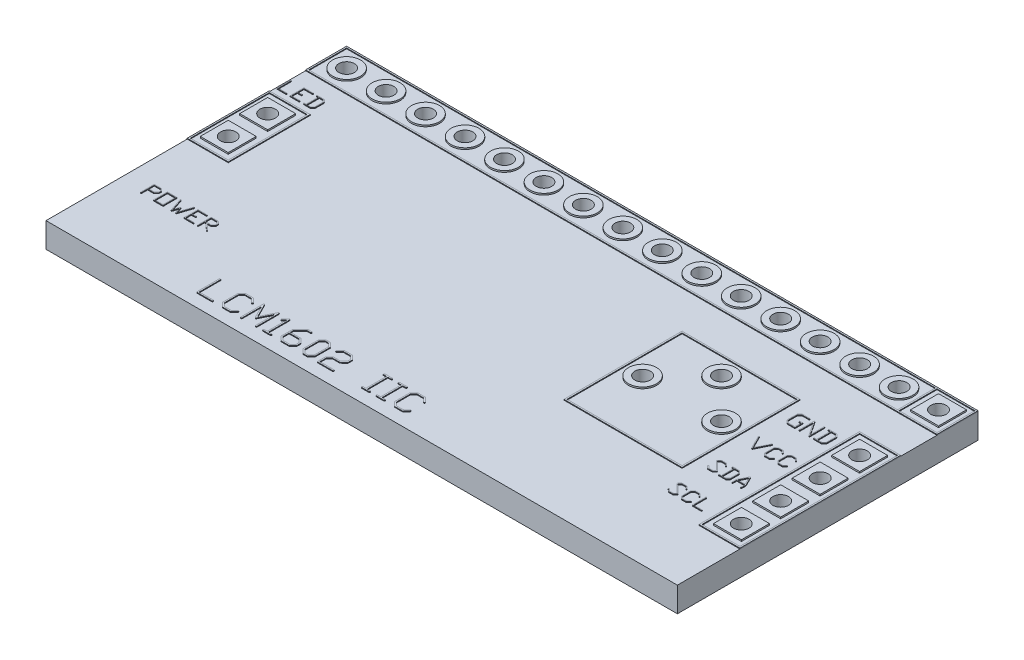
SolidWorks part; units mm, degrees
material "E-Glass Fiber"
ref_plane "Front Plane" through (0, 0, 0) normal (0, 0, 1) x (1, 0, 0)
ref_plane "Top Plane" through (0, 0, 0) normal (0, 1, 0) x (1, 0, 0)
ref_plane "Right Plane" through (0, 0, 0) normal (1, 0, 0) x (0, 0, -1)
sketch "Sketch2" plane through (0, 0, 0) normal (0, 1, 0) x (1, 0, 0)
  line L0 (-1.27, 1.27) -> (1.27, -1.27) construction
  line L1 (-1.27, 1.27) -> (1.27, 1.27)
  line L2 (-1.27, 1.27) -> (-1.27, -1.27)
  line L3 (-1.27, -1.27) -> (1.27, -1.27)
  line L4 (1.27, 1.27) -> (1.27, -1.27)
  line L5 (1.27, 1.27) -> (3.81, 1.27)
  line L6 (1.27, 1.27) -> (1.27, -1.27)
  line L7 (3.81, 1.27) -> (3.81, -1.27)
  line L8 (1.27, -1.27) -> (3.81, -1.27)
  line L9 (3.81, 1.27) -> (6.35, 1.27)
  line L10 (3.81, 1.27) -> (3.81, -1.27)
  line L11 (6.35, 1.27) -> (6.35, -1.27)
  line L12 (3.81, -1.27) -> (6.35, -1.27)
  line L13 (6.35, 1.27) -> (8.89, 1.27)
  line L14 (6.35, 1.27) -> (6.35, -1.27)
  line L15 (8.89, 1.27) -> (8.89, -1.27)
  line L16 (6.35, -1.27) -> (8.89, -1.27)
  line L17 (8.89, 1.27) -> (11.43, 1.27)
  line L18 (8.89, 1.27) -> (8.89, -1.27)
  line L19 (11.43, 1.27) -> (11.43, -1.27)
  line L20 (8.89, -1.27) -> (11.43, -1.27)
  line L21 (11.43, 1.27) -> (13.97, 1.27)
  line L22 (11.43, 1.27) -> (11.43, -1.27)
  line L23 (13.97, 1.27) -> (13.97, -1.27)
  line L24 (11.43, -1.27) -> (13.97, -1.27)
  line L25 (13.97, 1.27) -> (16.51, 1.27)
  line L26 (13.97, 1.27) -> (13.97, -1.27)
  line L27 (16.51, 1.27) -> (16.51, -1.27)
  line L28 (13.97, -1.27) -> (16.51, -1.27)
  line L29 (16.51, 1.27) -> (19.05, 1.27)
  line L30 (16.51, 1.27) -> (16.51, -1.27)
  line L31 (19.05, 1.27) -> (19.05, -1.27)
  line L32 (16.51, -1.27) -> (19.05, -1.27)
  line L33 (19.05, 1.27) -> (21.59, 1.27)
  line L34 (19.05, 1.27) -> (19.05, -1.27)
  line L35 (21.59, 1.27) -> (21.59, -1.27)
  line L36 (19.05, -1.27) -> (21.59, -1.27)
  line L37 (21.59, 1.27) -> (24.13, 1.27)
  line L38 (21.59, 1.27) -> (21.59, -1.27)
  line L39 (24.13, 1.27) -> (24.13, -1.27)
  line L40 (21.59, -1.27) -> (24.13, -1.27)
  line L41 (24.13, 1.27) -> (26.67, 1.27)
  line L42 (24.13, 1.27) -> (24.13, -1.27)
  line L43 (26.67, 1.27) -> (26.67, -1.27)
  line L44 (24.13, -1.27) -> (26.67, -1.27)
  line L45 (26.67, 1.27) -> (29.21, 1.27)
  line L46 (26.67, 1.27) -> (26.67, -1.27)
  line L47 (29.21, 1.27) -> (29.21, -1.27)
  line L48 (26.67, -1.27) -> (29.21, -1.27)
  line L49 (29.21, 1.27) -> (31.75, 1.27)
  line L50 (29.21, 1.27) -> (29.21, -1.27)
  line L51 (31.75, 1.27) -> (31.75, -1.27)
  line L52 (29.21, -1.27) -> (31.75, -1.27)
  line L53 (31.75, 1.27) -> (34.29, 1.27)
  line L54 (31.75, 1.27) -> (31.75, -1.27)
  line L55 (34.29, 1.27) -> (34.29, -1.27)
  line L56 (31.75, -1.27) -> (34.29, -1.27)
  line L57 (34.29, 1.27) -> (36.83, 1.27)
  line L58 (34.29, 1.27) -> (34.29, -1.27)
  line L59 (36.83, 1.27) -> (36.83, -1.27)
  line L60 (34.29, -1.27) -> (36.83, -1.27)
  line L61 (36.83, 1.27) -> (39.37, 1.27)
  line L62 (36.83, 1.27) -> (36.83, -1.27)
  line L63 (39.37, 1.27) -> (39.37, -1.27)
  line L64 (36.83, -1.27) -> (39.37, -1.27)
  line L65 (1.27, -1.27) -> (3.81, -1.27)
  line L66 (1.27, -1.27) -> (1.27, -3.81)
  line L67 (3.81, -1.27) -> (3.81, -3.81)
  line L68 (1.27, -3.81) -> (3.81, -3.81)
  line L69 (3.81, -1.27) -> (6.35, -1.27)
  line L70 (3.81, -1.27) -> (3.81, -3.81)
  line L71 (6.35, -1.27) -> (6.35, -3.81)
  line L72 (3.81, -3.81) -> (6.35, -3.81)
  line L73 (6.35, -1.27) -> (8.89, -1.27)
  line L74 (6.35, -1.27) -> (6.35, -3.81)
  line L75 (8.89, -1.27) -> (8.89, -3.81)
  line L76 (6.35, -3.81) -> (8.89, -3.81)
  line L77 (8.89, -1.27) -> (11.43, -1.27)
  line L78 (8.89, -1.27) -> (8.89, -3.81)
  line L79 (11.43, -1.27) -> (11.43, -3.81)
  line L80 (8.89, -3.81) -> (11.43, -3.81)
  line L81 (11.43, -1.27) -> (13.97, -1.27)
  line L82 (11.43, -1.27) -> (11.43, -3.81)
  line L83 (13.97, -1.27) -> (13.97, -3.81)
  line L84 (11.43, -3.81) -> (13.97, -3.81)
  line L85 (13.97, -1.27) -> (16.51, -1.27)
  line L86 (13.97, -1.27) -> (13.97, -3.81)
  line L87 (16.51, -1.27) -> (16.51, -3.81)
  line L88 (13.97, -3.81) -> (16.51, -3.81)
  line L89 (16.51, -1.27) -> (19.05, -1.27)
  line L90 (16.51, -1.27) -> (16.51, -3.81)
  line L91 (19.05, -1.27) -> (19.05, -3.81)
  line L92 (16.51, -3.81) -> (19.05, -3.81)
  line L93 (19.05, -1.27) -> (21.59, -1.27)
  line L94 (19.05, -1.27) -> (19.05, -3.81)
  line L95 (21.59, -1.27) -> (21.59, -3.81)
  line L96 (19.05, -3.81) -> (21.59, -3.81)
  line L97 (21.59, -1.27) -> (24.13, -1.27)
  line L98 (21.59, -1.27) -> (21.59, -3.81)
  line L99 (24.13, -1.27) -> (24.13, -3.81)
  line L100 (21.59, -3.81) -> (24.13, -3.81)
  line L101 (24.13, -1.27) -> (26.67, -1.27)
  line L102 (24.13, -1.27) -> (24.13, -3.81)
  line L103 (26.67, -1.27) -> (26.67, -3.81)
  line L104 (24.13, -3.81) -> (26.67, -3.81)
  line L105 (26.67, -1.27) -> (29.21, -1.27)
  line L106 (26.67, -1.27) -> (26.67, -3.81)
  line L107 (29.21, -1.27) -> (29.21, -3.81)
  line L108 (26.67, -3.81) -> (29.21, -3.81)
  line L109 (29.21, -1.27) -> (31.75, -1.27)
  line L110 (29.21, -1.27) -> (29.21, -3.81)
  line L111 (31.75, -1.27) -> (31.75, -3.81)
  line L112 (29.21, -3.81) -> (31.75, -3.81)
  line L113 (31.75, -1.27) -> (34.29, -1.27)
  line L114 (31.75, -1.27) -> (31.75, -3.81)
  line L115 (34.29, -1.27) -> (34.29, -3.81)
  line L116 (31.75, -3.81) -> (34.29, -3.81)
  line L117 (34.29, -1.27) -> (36.83, -1.27)
  line L118 (34.29, -1.27) -> (34.29, -3.81)
  line L119 (36.83, -1.27) -> (36.83, -3.81)
  line L120 (34.29, -3.81) -> (36.83, -3.81)
  line L121 (36.83, -1.27) -> (39.37, -1.27)
  line L122 (36.83, -1.27) -> (36.83, -3.81)
  line L123 (39.37, -1.27) -> (39.37, -3.81)
  line L124 (36.83, -3.81) -> (39.37, -3.81)
  line L125 (1.27, -3.81) -> (3.81, -3.81)
  line L126 (1.27, -3.81) -> (1.27, -6.35)
  line L127 (3.81, -3.81) -> (3.81, -6.35)
  line L128 (1.27, -6.35) -> (3.81, -6.35)
  line L129 (3.81, -3.81) -> (6.35, -3.81)
  line L130 (3.81, -3.81) -> (3.81, -6.35)
  line L131 (6.35, -3.81) -> (6.35, -6.35)
  line L132 (3.81, -6.35) -> (6.35, -6.35)
  line L133 (6.35, -3.81) -> (8.89, -3.81)
  line L134 (6.35, -3.81) -> (6.35, -6.35)
  line L135 (8.89, -3.81) -> (8.89, -6.35)
  line L136 (6.35, -6.35) -> (8.89, -6.35)
  line L137 (8.89, -3.81) -> (11.43, -3.81)
  line L138 (8.89, -3.81) -> (8.89, -6.35)
  line L139 (11.43, -3.81) -> (11.43, -6.35)
  line L140 (8.89, -6.35) -> (11.43, -6.35)
  line L141 (11.43, -3.81) -> (13.97, -3.81)
  line L142 (11.43, -3.81) -> (11.43, -6.35)
  line L143 (13.97, -3.81) -> (13.97, -6.35)
  line L144 (11.43, -6.35) -> (13.97, -6.35)
  line L145 (13.97, -3.81) -> (16.51, -3.81)
  line L146 (13.97, -3.81) -> (13.97, -6.35)
  line L147 (16.51, -3.81) -> (16.51, -6.35)
  line L148 (13.97, -6.35) -> (16.51, -6.35)
  line L149 (16.51, -3.81) -> (19.05, -3.81)
  line L150 (16.51, -3.81) -> (16.51, -6.35)
  line L151 (19.05, -3.81) -> (19.05, -6.35)
  line L152 (16.51, -6.35) -> (19.05, -6.35)
  line L153 (19.05, -3.81) -> (21.59, -3.81)
  line L154 (19.05, -3.81) -> (19.05, -6.35)
  line L155 (21.59, -3.81) -> (21.59, -6.35)
  line L156 (19.05, -6.35) -> (21.59, -6.35)
  line L157 (21.59, -3.81) -> (24.13, -3.81)
  line L158 (21.59, -3.81) -> (21.59, -6.35)
  line L159 (24.13, -3.81) -> (24.13, -6.35)
  line L160 (21.59, -6.35) -> (24.13, -6.35)
  line L161 (24.13, -3.81) -> (26.67, -3.81)
  line L162 (24.13, -3.81) -> (24.13, -6.35)
  line L163 (26.67, -3.81) -> (26.67, -6.35)
  line L164 (24.13, -6.35) -> (26.67, -6.35)
  line L165 (26.67, -3.81) -> (29.21, -3.81)
  line L166 (26.67, -3.81) -> (26.67, -6.35)
  line L167 (29.21, -3.81) -> (29.21, -6.35)
  line L168 (26.67, -6.35) -> (29.21, -6.35)
  line L169 (29.21, -3.81) -> (31.75, -3.81)
  line L170 (29.21, -3.81) -> (29.21, -6.35)
  line L171 (31.75, -3.81) -> (31.75, -6.35)
  line L172 (29.21, -6.35) -> (31.75, -6.35)
  line L173 (31.75, -3.81) -> (34.29, -3.81)
  line L174 (31.75, -3.81) -> (31.75, -6.35)
  line L175 (34.29, -3.81) -> (34.29, -6.35)
  line L176 (31.75, -6.35) -> (34.29, -6.35)
  line L177 (34.29, -3.81) -> (36.83, -3.81)
  line L178 (34.29, -3.81) -> (34.29, -6.35)
  line L179 (36.83, -3.81) -> (36.83, -6.35)
  line L180 (34.29, -6.35) -> (36.83, -6.35)
  line L181 (36.83, -3.81) -> (39.37, -3.81)
  line L182 (36.83, -3.81) -> (36.83, -6.35)
  line L183 (39.37, -3.81) -> (39.37, -6.35)
  line L184 (36.83, -6.35) -> (39.37, -6.35)
  line L185 (1.27, -6.35) -> (3.81, -6.35)
  line L186 (1.27, -6.35) -> (1.27, -8.89)
  line L187 (3.81, -6.35) -> (3.81, -8.89)
  line L188 (1.27, -8.89) -> (3.81, -8.89)
  line L189 (3.81, -6.35) -> (6.35, -6.35)
  line L190 (3.81, -6.35) -> (3.81, -8.89)
  line L191 (6.35, -6.35) -> (6.35, -8.89)
  line L192 (3.81, -8.89) -> (6.35, -8.89)
  line L193 (6.35, -6.35) -> (8.89, -6.35)
  line L194 (6.35, -6.35) -> (6.35, -8.89)
  line L195 (8.89, -6.35) -> (8.89, -8.89)
  line L196 (6.35, -8.89) -> (8.89, -8.89)
  line L197 (8.89, -6.35) -> (11.43, -6.35)
  line L198 (8.89, -6.35) -> (8.89, -8.89)
  line L199 (11.43, -6.35) -> (11.43, -8.89)
  line L200 (8.89, -8.89) -> (11.43, -8.89)
  line L201 (11.43, -6.35) -> (13.97, -6.35)
  line L202 (11.43, -6.35) -> (11.43, -8.89)
  line L203 (13.97, -6.35) -> (13.97, -8.89)
  line L204 (11.43, -8.89) -> (13.97, -8.89)
  line L205 (13.97, -6.35) -> (16.51, -6.35)
  line L206 (13.97, -6.35) -> (13.97, -8.89)
  line L207 (16.51, -6.35) -> (16.51, -8.89)
  line L208 (13.97, -8.89) -> (16.51, -8.89)
  line L209 (16.51, -6.35) -> (19.05, -6.35)
  line L210 (16.51, -6.35) -> (16.51, -8.89)
  line L211 (19.05, -6.35) -> (19.05, -8.89)
  line L212 (16.51, -8.89) -> (19.05, -8.89)
  line L213 (19.05, -6.35) -> (21.59, -6.35)
  line L214 (19.05, -6.35) -> (19.05, -8.89)
  line L215 (21.59, -6.35) -> (21.59, -8.89)
  line L216 (19.05, -8.89) -> (21.59, -8.89)
  line L217 (21.59, -6.35) -> (24.13, -6.35)
  line L218 (21.59, -6.35) -> (21.59, -8.89)
  line L219 (24.13, -6.35) -> (24.13, -8.89)
  line L220 (21.59, -8.89) -> (24.13, -8.89)
  line L221 (24.13, -6.35) -> (26.67, -6.35)
  line L222 (24.13, -6.35) -> (24.13, -8.89)
  line L223 (26.67, -6.35) -> (26.67, -8.89)
  line L224 (24.13, -8.89) -> (26.67, -8.89)
  line L225 (26.67, -6.35) -> (29.21, -6.35)
  line L226 (26.67, -6.35) -> (26.67, -8.89)
  line L227 (29.21, -6.35) -> (29.21, -8.89)
  line L228 (26.67, -8.89) -> (29.21, -8.89)
  line L229 (29.21, -6.35) -> (31.75, -6.35)
  line L230 (29.21, -6.35) -> (29.21, -8.89)
  line L231 (31.75, -6.35) -> (31.75, -8.89)
  line L232 (29.21, -8.89) -> (31.75, -8.89)
  line L233 (31.75, -6.35) -> (34.29, -6.35)
  line L234 (31.75, -6.35) -> (31.75, -8.89)
  line L235 (34.29, -6.35) -> (34.29, -8.89)
  line L236 (31.75, -8.89) -> (34.29, -8.89)
  line L237 (34.29, -6.35) -> (36.83, -6.35)
  line L238 (34.29, -6.35) -> (34.29, -8.89)
  line L239 (36.83, -6.35) -> (36.83, -8.89)
  line L240 (34.29, -8.89) -> (36.83, -8.89)
  line L241 (36.83, -6.35) -> (39.37, -6.35)
  line L242 (36.83, -6.35) -> (36.83, -8.89)
  line L243 (39.37, -6.35) -> (39.37, -8.89)
  line L244 (36.83, -8.89) -> (39.37, -8.89)
  line L245 (1.27, -8.89) -> (3.81, -8.89)
  line L246 (1.27, -8.89) -> (1.27, -11.43)
  line L247 (3.81, -8.89) -> (3.81, -11.43)
  line L248 (1.27, -11.43) -> (3.81, -11.43)
  line L249 (3.81, -8.89) -> (6.35, -8.89)
  line L250 (3.81, -8.89) -> (3.81, -11.43)
  line L251 (6.35, -8.89) -> (6.35, -11.43)
  line L252 (3.81, -11.43) -> (6.35, -11.43)
  line L253 (6.35, -8.89) -> (8.89, -8.89)
  line L254 (6.35, -8.89) -> (6.35, -11.43)
  line L255 (8.89, -8.89) -> (8.89, -11.43)
  line L256 (6.35, -11.43) -> (8.89, -11.43)
  line L257 (8.89, -8.89) -> (11.43, -8.89)
  line L258 (8.89, -8.89) -> (8.89, -11.43)
  line L259 (11.43, -8.89) -> (11.43, -11.43)
  line L260 (8.89, -11.43) -> (11.43, -11.43)
  line L261 (11.43, -8.89) -> (13.97, -8.89)
  line L262 (11.43, -8.89) -> (11.43, -11.43)
  line L263 (13.97, -8.89) -> (13.97, -11.43)
  line L264 (11.43, -11.43) -> (13.97, -11.43)
  line L265 (13.97, -8.89) -> (16.51, -8.89)
  line L266 (13.97, -8.89) -> (13.97, -11.43)
  line L267 (16.51, -8.89) -> (16.51, -11.43)
  line L268 (13.97, -11.43) -> (16.51, -11.43)
  line L269 (16.51, -8.89) -> (19.05, -8.89)
  line L270 (16.51, -8.89) -> (16.51, -11.43)
  line L271 (19.05, -8.89) -> (19.05, -11.43)
  line L272 (16.51, -11.43) -> (19.05, -11.43)
  line L273 (19.05, -8.89) -> (21.59, -8.89)
  line L274 (19.05, -8.89) -> (19.05, -11.43)
  line L275 (21.59, -8.89) -> (21.59, -11.43)
  line L276 (19.05, -11.43) -> (21.59, -11.43)
  line L277 (21.59, -8.89) -> (24.13, -8.89)
  line L278 (21.59, -8.89) -> (21.59, -11.43)
  line L279 (24.13, -8.89) -> (24.13, -11.43)
  line L280 (21.59, -11.43) -> (24.13, -11.43)
  line L281 (24.13, -8.89) -> (26.67, -8.89)
  line L282 (24.13, -8.89) -> (24.13, -11.43)
  line L283 (26.67, -8.89) -> (26.67, -11.43)
  line L284 (24.13, -11.43) -> (26.67, -11.43)
  line L285 (26.67, -8.89) -> (29.21, -8.89)
  line L286 (26.67, -8.89) -> (26.67, -11.43)
  line L287 (29.21, -8.89) -> (29.21, -11.43)
  line L288 (26.67, -11.43) -> (29.21, -11.43)
  line L289 (29.21, -8.89) -> (31.75, -8.89)
  line L290 (29.21, -8.89) -> (29.21, -11.43)
  line L291 (31.75, -8.89) -> (31.75, -11.43)
  line L292 (29.21, -11.43) -> (31.75, -11.43)
  line L293 (31.75, -8.89) -> (34.29, -8.89)
  line L294 (31.75, -8.89) -> (31.75, -11.43)
  line L295 (34.29, -8.89) -> (34.29, -11.43)
  line L296 (31.75, -11.43) -> (34.29, -11.43)
  line L297 (34.29, -8.89) -> (36.83, -8.89)
  line L298 (34.29, -8.89) -> (34.29, -11.43)
  line L299 (36.83, -8.89) -> (36.83, -11.43)
  line L300 (34.29, -11.43) -> (36.83, -11.43)
  line L301 (36.83, -8.89) -> (39.37, -8.89)
  line L302 (36.83, -8.89) -> (36.83, -11.43)
  line L303 (39.37, -8.89) -> (39.37, -11.43)
  line L304 (36.83, -11.43) -> (39.37, -11.43)
  line L305 (1.27, -11.43) -> (3.81, -11.43)
  line L306 (1.27, -11.43) -> (1.27, -13.97)
  line L307 (3.81, -11.43) -> (3.81, -13.97)
  line L308 (1.27, -13.97) -> (3.81, -13.97)
  line L309 (3.81, -11.43) -> (6.35, -11.43)
  line L310 (3.81, -11.43) -> (3.81, -13.97)
  line L311 (6.35, -11.43) -> (6.35, -13.97)
  line L312 (3.81, -13.97) -> (6.35, -13.97)
  line L313 (6.35, -11.43) -> (8.89, -11.43)
  line L314 (6.35, -11.43) -> (6.35, -13.97)
  line L315 (8.89, -11.43) -> (8.89, -13.97)
  line L316 (6.35, -13.97) -> (8.89, -13.97)
  line L317 (8.89, -11.43) -> (11.43, -11.43)
  line L318 (8.89, -11.43) -> (8.89, -13.97)
  line L319 (11.43, -11.43) -> (11.43, -13.97)
  line L320 (8.89, -13.97) -> (11.43, -13.97)
  line L321 (11.43, -11.43) -> (13.97, -11.43)
  line L322 (11.43, -11.43) -> (11.43, -13.97)
  line L323 (13.97, -11.43) -> (13.97, -13.97)
  line L324 (11.43, -13.97) -> (13.97, -13.97)
  line L325 (13.97, -11.43) -> (16.51, -11.43)
  line L326 (13.97, -11.43) -> (13.97, -13.97)
  line L327 (16.51, -11.43) -> (16.51, -13.97)
  line L328 (13.97, -13.97) -> (16.51, -13.97)
  line L329 (16.51, -11.43) -> (19.05, -11.43)
  line L330 (16.51, -11.43) -> (16.51, -13.97)
  line L331 (19.05, -11.43) -> (19.05, -13.97)
  line L332 (16.51, -13.97) -> (19.05, -13.97)
  line L333 (19.05, -11.43) -> (21.59, -11.43)
  line L334 (19.05, -11.43) -> (19.05, -13.97)
  line L335 (21.59, -11.43) -> (21.59, -13.97)
  line L336 (19.05, -13.97) -> (21.59, -13.97)
  line L337 (21.59, -11.43) -> (24.13, -11.43)
  line L338 (21.59, -11.43) -> (21.59, -13.97)
  line L339 (24.13, -11.43) -> (24.13, -13.97)
  line L340 (21.59, -13.97) -> (24.13, -13.97)
  line L341 (24.13, -11.43) -> (26.67, -11.43)
  line L342 (24.13, -11.43) -> (24.13, -13.97)
  line L343 (26.67, -11.43) -> (26.67, -13.97)
  line L344 (24.13, -13.97) -> (26.67, -13.97)
  line L345 (26.67, -11.43) -> (29.21, -11.43)
  line L346 (26.67, -11.43) -> (26.67, -13.97)
  line L347 (29.21, -11.43) -> (29.21, -13.97)
  line L348 (26.67, -13.97) -> (29.21, -13.97)
  line L349 (29.21, -11.43) -> (31.75, -11.43)
  line L350 (29.21, -11.43) -> (29.21, -13.97)
  line L351 (31.75, -11.43) -> (31.75, -13.97)
  line L352 (29.21, -13.97) -> (31.75, -13.97)
  line L353 (31.75, -11.43) -> (34.29, -11.43)
  line L354 (31.75, -11.43) -> (31.75, -13.97)
  line L355 (34.29, -11.43) -> (34.29, -13.97)
  line L356 (31.75, -13.97) -> (34.29, -13.97)
  line L357 (34.29, -11.43) -> (36.83, -11.43)
  line L358 (34.29, -11.43) -> (34.29, -13.97)
  line L359 (36.83, -11.43) -> (36.83, -13.97)
  line L360 (34.29, -13.97) -> (36.83, -13.97)
  line L361 (36.83, -11.43) -> (39.37, -11.43)
  line L362 (36.83, -11.43) -> (36.83, -13.97)
  line L363 (39.37, -11.43) -> (39.37, -13.97)
  line L364 (36.83, -13.97) -> (39.37, -13.97)
  line L365 (1.27, -13.97) -> (3.81, -13.97)
  line L366 (1.27, -13.97) -> (1.27, -16.51)
  line L367 (3.81, -13.97) -> (3.81, -16.51)
  line L368 (1.27, -16.51) -> (3.81, -16.51)
  line L369 (3.81, -13.97) -> (6.35, -13.97)
  line L370 (3.81, -13.97) -> (3.81, -16.51)
  line L371 (6.35, -13.97) -> (6.35, -16.51)
  line L372 (3.81, -16.51) -> (6.35, -16.51)
  line L373 (6.35, -13.97) -> (8.89, -13.97)
  line L374 (6.35, -13.97) -> (6.35, -16.51)
  line L375 (8.89, -13.97) -> (8.89, -16.51)
  line L376 (6.35, -16.51) -> (8.89, -16.51)
  line L377 (8.89, -13.97) -> (11.43, -13.97)
  line L378 (8.89, -13.97) -> (8.89, -16.51)
  line L379 (11.43, -13.97) -> (11.43, -16.51)
  line L380 (8.89, -16.51) -> (11.43, -16.51)
  line L381 (11.43, -13.97) -> (13.97, -13.97)
  line L382 (11.43, -13.97) -> (11.43, -16.51)
  line L383 (13.97, -13.97) -> (13.97, -16.51)
  line L384 (11.43, -16.51) -> (13.97, -16.51)
  line L385 (13.97, -13.97) -> (16.51, -13.97)
  line L386 (13.97, -13.97) -> (13.97, -16.51)
  line L387 (16.51, -13.97) -> (16.51, -16.51)
  line L388 (13.97, -16.51) -> (16.51, -16.51)
  line L389 (16.51, -13.97) -> (19.05, -13.97)
  line L390 (16.51, -13.97) -> (16.51, -16.51)
  line L391 (19.05, -13.97) -> (19.05, -16.51)
  line L392 (16.51, -16.51) -> (19.05, -16.51)
  line L393 (19.05, -13.97) -> (21.59, -13.97)
  line L394 (19.05, -13.97) -> (19.05, -16.51)
  line L395 (21.59, -13.97) -> (21.59, -16.51)
  line L396 (19.05, -16.51) -> (21.59, -16.51)
  line L397 (21.59, -13.97) -> (24.13, -13.97)
  line L398 (21.59, -13.97) -> (21.59, -16.51)
  line L399 (24.13, -13.97) -> (24.13, -16.51)
  line L400 (21.59, -16.51) -> (24.13, -16.51)
  line L401 (24.13, -13.97) -> (26.67, -13.97)
  line L402 (24.13, -13.97) -> (24.13, -16.51)
  line L403 (26.67, -13.97) -> (26.67, -16.51)
  line L404 (24.13, -16.51) -> (26.67, -16.51)
  line L405 (26.67, -13.97) -> (29.21, -13.97)
  line L406 (26.67, -13.97) -> (26.67, -16.51)
  line L407 (29.21, -13.97) -> (29.21, -16.51)
  line L408 (26.67, -16.51) -> (29.21, -16.51)
  line L409 (29.21, -13.97) -> (31.75, -13.97)
  line L410 (29.21, -13.97) -> (29.21, -16.51)
  line L411 (31.75, -13.97) -> (31.75, -16.51)
  line L412 (29.21, -16.51) -> (31.75, -16.51)
  line L413 (31.75, -13.97) -> (34.29, -13.97)
  line L414 (31.75, -13.97) -> (31.75, -16.51)
  line L415 (34.29, -13.97) -> (34.29, -16.51)
  line L416 (31.75, -16.51) -> (34.29, -16.51)
  line L417 (34.29, -13.97) -> (36.83, -13.97)
  line L418 (34.29, -13.97) -> (34.29, -16.51)
  line L419 (36.83, -13.97) -> (36.83, -16.51)
  line L420 (34.29, -16.51) -> (36.83, -16.51)
  line L421 (36.83, -13.97) -> (39.37, -13.97)
  line L422 (36.83, -13.97) -> (36.83, -16.51)
  line L423 (39.37, -13.97) -> (39.37, -16.51)
  line L424 (36.83, -16.51) -> (39.37, -16.51)
  line L425 (1.27, -16.51) -> (3.81, -16.51)
  line L426 (1.27, -16.51) -> (1.27, -19.05)
  line L427 (3.81, -16.51) -> (3.81, -19.05)
  line L428 (1.27, -19.05) -> (3.81, -19.05)
  line L429 (3.81, -16.51) -> (6.35, -16.51)
  line L430 (3.81, -16.51) -> (3.81, -19.05)
  line L431 (6.35, -16.51) -> (6.35, -19.05)
  line L432 (3.81, -19.05) -> (6.35, -19.05)
  line L433 (6.35, -16.51) -> (8.89, -16.51)
  line L434 (6.35, -16.51) -> (6.35, -19.05)
  line L435 (8.89, -16.51) -> (8.89, -19.05)
  line L436 (6.35, -19.05) -> (8.89, -19.05)
  line L437 (8.89, -16.51) -> (11.43, -16.51)
  line L438 (8.89, -16.51) -> (8.89, -19.05)
  line L439 (11.43, -16.51) -> (11.43, -19.05)
  line L440 (8.89, -19.05) -> (11.43, -19.05)
  line L441 (11.43, -16.51) -> (13.97, -16.51)
  line L442 (11.43, -16.51) -> (11.43, -19.05)
  line L443 (13.97, -16.51) -> (13.97, -19.05)
  line L444 (11.43, -19.05) -> (13.97, -19.05)
  line L445 (13.97, -16.51) -> (16.51, -16.51)
  line L446 (13.97, -16.51) -> (13.97, -19.05)
  line L447 (16.51, -16.51) -> (16.51, -19.05)
  line L448 (13.97, -19.05) -> (16.51, -19.05)
  line L449 (16.51, -16.51) -> (19.05, -16.51)
  line L450 (16.51, -16.51) -> (16.51, -19.05)
  line L451 (19.05, -16.51) -> (19.05, -19.05)
  line L452 (16.51, -19.05) -> (19.05, -19.05)
  line L453 (19.05, -16.51) -> (21.59, -16.51)
  line L454 (19.05, -16.51) -> (19.05, -19.05)
  line L455 (21.59, -16.51) -> (21.59, -19.05)
  line L456 (19.05, -19.05) -> (21.59, -19.05)
  line L457 (21.59, -16.51) -> (24.13, -16.51)
  line L458 (21.59, -16.51) -> (21.59, -19.05)
  line L459 (24.13, -16.51) -> (24.13, -19.05)
  line L460 (21.59, -19.05) -> (24.13, -19.05)
  line L461 (24.13, -16.51) -> (26.67, -16.51)
  line L462 (24.13, -16.51) -> (24.13, -19.05)
  line L463 (26.67, -16.51) -> (26.67, -19.05)
  line L464 (24.13, -19.05) -> (26.67, -19.05)
  line L465 (26.67, -16.51) -> (29.21, -16.51)
  line L466 (26.67, -16.51) -> (26.67, -19.05)
  line L467 (29.21, -16.51) -> (29.21, -19.05)
  line L468 (26.67, -19.05) -> (29.21, -19.05)
  line L469 (29.21, -16.51) -> (31.75, -16.51)
  line L470 (29.21, -16.51) -> (29.21, -19.05)
  line L471 (31.75, -16.51) -> (31.75, -19.05)
  line L472 (29.21, -19.05) -> (31.75, -19.05)
  line L473 (31.75, -16.51) -> (34.29, -16.51)
  line L474 (31.75, -16.51) -> (31.75, -19.05)
  line L475 (34.29, -16.51) -> (34.29, -19.05)
  line L476 (31.75, -19.05) -> (34.29, -19.05)
  line L477 (34.29, -16.51) -> (36.83, -16.51)
  line L478 (34.29, -16.51) -> (34.29, -19.05)
  line L479 (36.83, -16.51) -> (36.83, -19.05)
  line L480 (34.29, -19.05) -> (36.83, -19.05)
  line L481 (36.83, -16.51) -> (39.37, -16.51)
  line L482 (36.83, -16.51) -> (36.83, -19.05)
  line L483 (39.37, -16.51) -> (39.37, -19.05)
  line L484 (36.83, -19.05) -> (39.37, -19.05)
  line L485 (-1.27, -1.27) -> (1.27, -1.27)
  line L486 (-1.27, -1.27) -> (-1.27, -3.81)
  line L487 (1.27, -1.27) -> (1.27, -3.81)
  line L488 (-1.27, -3.81) -> (1.27, -3.81)
  line L489 (-1.27, -3.81) -> (1.27, -3.81)
  line L490 (-1.27, -3.81) -> (-1.27, -6.35)
  line L491 (1.27, -3.81) -> (1.27, -6.35)
  line L492 (-1.27, -6.35) -> (1.27, -6.35)
  line L493 (-1.27, -6.35) -> (1.27, -6.35)
  line L494 (-1.27, -6.35) -> (-1.27, -8.89)
  line L495 (1.27, -6.35) -> (1.27, -8.89)
  line L496 (-1.27, -8.89) -> (1.27, -8.89)
  line L497 (-1.27, -8.89) -> (1.27, -8.89)
  line L498 (-1.27, -8.89) -> (-1.27, -11.43)
  line L499 (1.27, -8.89) -> (1.27, -11.43)
  line L500 (-1.27, -11.43) -> (1.27, -11.43)
  line L501 (-1.27, -11.43) -> (1.27, -11.43)
  line L502 (-1.27, -11.43) -> (-1.27, -13.97)
  line L503 (1.27, -11.43) -> (1.27, -13.97)
  line L504 (-1.27, -13.97) -> (1.27, -13.97)
  line L505 (-1.27, -13.97) -> (1.27, -13.97)
  line L506 (-1.27, -13.97) -> (-1.27, -16.51)
  line L507 (1.27, -13.97) -> (1.27, -16.51)
  line L508 (-1.27, -16.51) -> (1.27, -16.51)
  line L509 (-1.27, -16.51) -> (1.27, -16.51)
  line L510 (-1.27, -16.51) -> (-1.27, -19.05)
  line L511 (1.27, -16.51) -> (1.27, -19.05)
  line L512 (-1.27, -19.05) -> (1.27, -19.05)
  line L513 (-1.27, 1.27) -> (1.27, 1.27) construction
  line L514 (-1.27, 1.27) -> (-1.27, -1.27) construction
  line L515 (0, -11.176) -> (0, 11.176) construction
  line L516 (-22.352, 0) -> (22.352, 0) construction
  circle A0 centre (0, 0) radius 0.5
  circle A1 centre (2.54, 0) radius 0.5
  circle A2 centre (5.08, 0) radius 0.5
  circle A3 centre (7.62, 0) radius 0.5
  circle A4 centre (10.16, 0) radius 0.5
  circle A5 centre (12.7, 0) radius 0.5
  circle A6 centre (15.24, 0) radius 0.5
  circle A7 centre (17.78, 0) radius 0.5
  circle A8 centre (20.32, 0) radius 0.5
  circle A9 centre (22.86, 0) radius 0.5
  circle A10 centre (25.4, 0) radius 0.5
  circle A11 centre (27.94, 0) radius 0.5
  circle A12 centre (30.48, 0) radius 0.5
  circle A13 centre (33.02, 0) radius 0.5
  circle A14 centre (35.56, 0) radius 0.5
  circle A15 centre (38.1, 0) radius 0.5
  circle A16 centre (2.54, -2.54) radius 0.5
  circle A17 centre (5.08, -2.54) radius 0.5
  circle A18 centre (7.62, -2.54) radius 0.5
  circle A19 centre (10.16, -2.54) radius 0.5
  circle A20 centre (12.7, -2.54) radius 0.5
  circle A21 centre (15.24, -2.54) radius 0.5
  circle A22 centre (17.78, -2.54) radius 0.5
  circle A23 centre (20.32, -2.54) radius 0.5
  circle A24 centre (22.86, -2.54) radius 0.5
  circle A25 centre (25.4, -2.54) radius 0.5
  circle A26 centre (27.94, -2.54) radius 0.5
  circle A27 centre (30.48, -2.54) radius 0.5
  circle A28 centre (33.02, -2.54) radius 0.5
  circle A29 centre (35.56, -2.54) radius 0.5
  circle A30 centre (38.1, -2.54) radius 0.5
  circle A31 centre (2.54, -5.08) radius 0.5
  circle A32 centre (5.08, -5.08) radius 0.5
  circle A33 centre (7.62, -5.08) radius 0.5
  circle A34 centre (10.16, -5.08) radius 0.5
  circle A35 centre (12.7, -5.08) radius 0.5
  circle A36 centre (15.24, -5.08) radius 0.5
  circle A37 centre (17.78, -5.08) radius 0.5
  circle A38 centre (20.32, -5.08) radius 0.5
  circle A39 centre (22.86, -5.08) radius 0.5
  circle A40 centre (25.4, -5.08) radius 0.5
  circle A41 centre (27.94, -5.08) radius 0.5
  circle A42 centre (30.48, -5.08) radius 0.5
  circle A43 centre (33.02, -5.08) radius 0.5
  circle A44 centre (35.56, -5.08) radius 0.5
  circle A45 centre (38.1, -5.08) radius 0.5
  circle A46 centre (2.54, -7.62) radius 0.5
  circle A47 centre (5.08, -7.62) radius 0.5
  circle A48 centre (7.62, -7.62) radius 0.5
  circle A49 centre (10.16, -7.62) radius 0.5
  circle A50 centre (12.7, -7.62) radius 0.5
  circle A51 centre (15.24, -7.62) radius 0.5
  circle A52 centre (17.78, -7.62) radius 0.5
  circle A53 centre (20.32, -7.62) radius 0.5
  circle A54 centre (22.86, -7.62) radius 0.5
  circle A55 centre (25.4, -7.62) radius 0.5
  circle A56 centre (27.94, -7.62) radius 0.5
  circle A57 centre (30.48, -7.62) radius 0.5
  circle A58 centre (33.02, -7.62) radius 0.5
  circle A59 centre (35.56, -7.62) radius 0.5
  circle A60 centre (38.1, -7.62) radius 0.5
  circle A61 centre (2.54, -10.16) radius 0.5
  circle A62 centre (5.08, -10.16) radius 0.5
  circle A63 centre (7.62, -10.16) radius 0.5
  circle A64 centre (10.16, -10.16) radius 0.5
  circle A65 centre (12.7, -10.16) radius 0.5
  circle A66 centre (15.24, -10.16) radius 0.5
  circle A67 centre (17.78, -10.16) radius 0.5
  circle A68 centre (20.32, -10.16) radius 0.5
  circle A69 centre (22.86, -10.16) radius 0.5
  circle A70 centre (25.4, -10.16) radius 0.5
  circle A71 centre (27.94, -10.16) radius 0.5
  circle A72 centre (30.48, -10.16) radius 0.5
  circle A73 centre (33.02, -10.16) radius 0.5
  circle A74 centre (35.56, -10.16) radius 0.5
  circle A75 centre (38.1, -10.16) radius 0.5
  circle A76 centre (2.54, -12.7) radius 0.5
  circle A77 centre (5.08, -12.7) radius 0.5
  circle A78 centre (7.62, -12.7) radius 0.5
  circle A79 centre (10.16, -12.7) radius 0.5
  circle A80 centre (12.7, -12.7) radius 0.5
  circle A81 centre (15.24, -12.7) radius 0.5
  circle A82 centre (17.78, -12.7) radius 0.5
  circle A83 centre (20.32, -12.7) radius 0.5
  circle A84 centre (22.86, -12.7) radius 0.5
  circle A85 centre (25.4, -12.7) radius 0.5
  circle A86 centre (27.94, -12.7) radius 0.5
  circle A87 centre (30.48, -12.7) radius 0.5
  circle A88 centre (33.02, -12.7) radius 0.5
  circle A89 centre (35.56, -12.7) radius 0.5
  circle A90 centre (38.1, -12.7) radius 0.5
  circle A91 centre (2.54, -15.24) radius 0.5
  circle A92 centre (5.08, -15.24) radius 0.5
  circle A93 centre (7.62, -15.24) radius 0.5
  circle A94 centre (10.16, -15.24) radius 0.5
  circle A95 centre (12.7, -15.24) radius 0.5
  circle A96 centre (15.24, -15.24) radius 0.5
  circle A97 centre (17.78, -15.24) radius 0.5
  circle A98 centre (20.32, -15.24) radius 0.5
  circle A99 centre (22.86, -15.24) radius 0.5
  circle A100 centre (25.4, -15.24) radius 0.5
  circle A101 centre (27.94, -15.24) radius 0.5
  circle A102 centre (30.48, -15.24) radius 0.5
  circle A103 centre (33.02, -15.24) radius 0.5
  circle A104 centre (35.56, -15.24) radius 0.5
  circle A105 centre (38.1, -15.24) radius 0.5
  circle A106 centre (2.54, -17.78) radius 0.5
  circle A107 centre (5.08, -17.78) radius 0.5
  circle A108 centre (7.62, -17.78) radius 0.5
  circle A109 centre (10.16, -17.78) radius 0.5
  circle A110 centre (12.7, -17.78) radius 0.5
  circle A111 centre (15.24, -17.78) radius 0.5
  circle A112 centre (17.78, -17.78) radius 0.5
  circle A113 centre (20.32, -17.78) radius 0.5
  circle A114 centre (22.86, -17.78) radius 0.5
  circle A115 centre (25.4, -17.78) radius 0.5
  circle A116 centre (27.94, -17.78) radius 0.5
  circle A117 centre (30.48, -17.78) radius 0.5
  circle A118 centre (33.02, -17.78) radius 0.5
  circle A119 centre (35.56, -17.78) radius 0.5
  circle A120 centre (38.1, -17.78) radius 0.5
  circle A121 centre (0, -2.54) radius 0.5
  circle A122 centre (0, -5.08) radius 0.5
  circle A123 centre (0, -7.62) radius 0.5
  circle A124 centre (0, -10.16) radius 0.5
  circle A125 centre (0, -12.7) radius 0.5
  circle A126 centre (0, -15.24) radius 0.5
  circle A127 centre (0, -17.78) radius 0.5
  dimension "D2" = 1
  dimension "D1" = 2.54
  dimension "D5" = 2.54
  dimension "D6" = 2.54
  dimension "D3" = 16
  dimension "D4" = 8
sketch "Sketch3" plane through (0, 0, 0) normal (0, 1, 0) x (1, 0, 0)
  line L0 (39.37, -16.51) -> (39.37, -19.05) construction
  line L1 (-1.27, 1.27) -> (39.37, 1.27)
  line L2 (-1.27, 1.27) -> (-1.27, -18.08)
  line L3 (-1.27, -18.08) -> (39.37, -18.08)
  line L4 (39.37, 1.27) -> (39.37, -18.08)
  dimension "D1" = 19.35
extrude "Boss-Extrude1" add sketch "Sketch3" along normal blind 1.6
sketch "Sketch9" plane through (0, 0, 0) normal (0, 1, 0) x (1, 0, 0)
  line L0 (0, 0) -> (2.54, 0) construction
  line L1 (-0.88, 0) -> (0.88, 0) construction
  circle A0 centre (0, 0) radius 0.5
  circle A1 centre (2.54, 0) radius 0.5
  circle A2 centre (5.08, 0) radius 0.5
  circle A3 centre (7.62, 0) radius 0.5
  circle A4 centre (10.16, 0) radius 0.5
  circle A5 centre (12.7, 0) radius 0.5
  circle A6 centre (15.24, 0) radius 0.5
  circle A7 centre (17.78, 0) radius 0.5
  circle A8 centre (20.32, 0) radius 0.5
  circle A9 centre (22.86, 0) radius 0.5
  circle A10 centre (25.4, 0) radius 0.5
  circle A11 centre (27.94, 0) radius 0.5
  circle A12 centre (30.48, 0) radius 0.5
  circle A13 centre (33.02, 0) radius 0.5
  circle A14 centre (35.56, 0) radius 0.5
  circle A15 centre (38.1, 0) radius 0.5
  dimension "D1" = 1
  dimension "D3" = 2.54
  dimension "D2" = 16
extrude "Cut-Extrude1" cut sketch "Sketch9" along normal through all
sketch "Sketch10" plane through (0, 0, 0) normal (0, 1, 0) x (1, 0, 0)
  line L0 (0, -0.88) -> (0, 0.88) construction
  line L1 (-0.88, 0) -> (0.88, 0) construction
  circle A0 centre (0, -5.08) radius 0.5
  circle A1 centre (0, -7.62) radius 0.5
  dimension "D1" = 1
  dimension "D3" = 5.08
  dimension "D2" = 2.54
extrude "Cut-Extrude2" cut sketch "Sketch10" along normal through all
sketch "Sketch12" plane through (0, 1.6, 0) normal (0, 1, 0) x (1, 0, 0)
  line L0 (0, -0.88) -> (0, 0.88) construction
  line L1 (-0.88, 0) -> (0.88, 0) construction
  circle A0 centre (38.1, -5.08) radius 0.5
  circle A1 centre (38.1, -7.62) radius 0.5
  circle A2 centre (38.1, -10.16) radius 0.5
  circle A3 centre (38.1, -12.7) radius 0.5
  dimension "D1" = 1
  dimension "D2" = 38.1
  dimension "D3" = 2.54
  dimension "D4" = 2.54
  dimension "D5" = 2.54
  dimension "D6" = 5.08
extrude "Cut-Extrude3" cut sketch "Sketch12" against normal through all
sketch "Sketch13" plane through (0, 0, 0) normal (0, 1, 0) x (1, 0, 0)
  line L0 (0, -0.88) -> (0, 0.88) construction
  line L1 (-0.88, 0) -> (0.88, 0) construction
  circle A0 centre (29.21, -5.08) radius 0.5
  circle A1 centre (26.67, -7.62) radius 0.5
  circle A2 centre (31.75, -7.62) radius 0.5
  dimension "D5" = 1
  dimension "D1" = 5.08
  dimension "D2" = 2.54
  dimension "D3" = 2.54
  dimension "D4" = 29.21
  dimension "D6" = 5.08
extrude "Cut-Extrude4" cut sketch "Sketch13" along normal through all
sketch "Sketch14" plane through (0, 1.6, 0) normal (0, 1, 0) x (1, 0, 0)
  line L0 (-0.88, 0) -> (0.88, 0) construction
  line L1 (37.2, 0.9) -> (39, 0.9)
  line L2 (37.2, 0.9) -> (37.2, -0.9)
  line L3 (37.2, -0.9) -> (39, -0.9)
  line L4 (39, 0.9) -> (39, -0.9)
  line L5 (0, -0.88) -> (0, 0.88) construction
  line L6 (-0.9, -4.18) -> (0.9, -4.18)
  line L7 (-0.9, -4.18) -> (-0.9, -5.98)
  line L8 (-0.9, -5.98) -> (0.9, -5.98)
  line L9 (0.9, -4.18) -> (0.9, -5.98)
  line L10 (37.2, -4.18) -> (39, -4.18)
  line L11 (37.2, -4.18) -> (37.2, -5.98)
  line L12 (37.2, -5.98) -> (39, -5.98)
  line L13 (39, -4.18) -> (39, -5.98)
  line L14 (-0.9, -6.72) -> (0.9, -6.72)
  line L15 (-0.9, -6.72) -> (-0.9, -8.52)
  line L16 (-0.9, -8.52) -> (0.9, -8.52)
  line L17 (0.9, -6.72) -> (0.9, -8.52)
  line L18 (37.2, -6.72) -> (39, -6.72)
  line L19 (37.2, -6.72) -> (37.2, -8.52)
  line L20 (37.2, -8.52) -> (39, -8.52)
  line L21 (39, -6.72) -> (39, -8.52)
  line L22 (37.2, -9.26) -> (39, -9.26)
  line L23 (37.2, -9.26) -> (37.2, -11.06)
  line L24 (37.2, -11.06) -> (39, -11.06)
  line L25 (39, -9.26) -> (39, -11.06)
  line L26 (37.2, -11.784) -> (39, -11.784)
  line L27 (37.2, -11.784) -> (37.2, -13.584)
  line L28 (37.2, -13.584) -> (39, -13.584)
  line L29 (39, -11.784) -> (39, -13.584)
  circle A0 centre (35.56, 0) radius 0.9
  circle A1 centre (38.1, 0) radius 0.5 construction
  circle A2 centre (33.02, 0) radius 0.9
  circle A3 centre (30.48, 0) radius 0.9
  circle A4 centre (27.94, 0) radius 0.9
  circle A5 centre (25.4, 0) radius 0.9
  circle A6 centre (22.86, 0) radius 0.9
  circle A7 centre (20.32, 0) radius 0.9
  circle A8 centre (17.78, 0) radius 0.9
  circle A9 centre (15.24, 0) radius 0.9
  circle A10 centre (12.7, 0) radius 0.9
  circle A11 centre (10.16, 0) radius 0.9
  circle A12 centre (7.62, 0) radius 0.9
  circle A13 centre (5.08, 0) radius 0.9
  circle A14 centre (2.54, 0) radius 0.9
  circle A15 centre (0, 0) radius 0.9
  circle A16 centre (29.21, -5.08) radius 0.9
  circle A17 centre (26.67, -7.62) radius 0.9
  circle A18 centre (31.75, -7.62) radius 0.9
  circle A19 centre (30.48, 0) radius 0.5 construction
  circle A20 centre (38.1, 0) radius 0.5
  circle A21 centre (35.56, 0) radius 0.5
  circle A22 centre (33.02, 0) radius 0.5
  circle A23 centre (30.48, 0) radius 0.5
  circle A24 centre (27.94, 0) radius 0.5
  circle A25 centre (25.4, 0) radius 0.5
  circle A26 centre (22.86, 0) radius 0.5
  circle A27 centre (20.32, 0) radius 0.5
  circle A28 centre (17.78, 0) radius 0.5
  circle A29 centre (15.24, 0) radius 0.5
  circle A30 centre (12.7, 0) radius 0.5
  circle A31 centre (10.16, 0) radius 0.5
  circle A32 centre (7.62, 0) radius 0.5
  circle A33 centre (5.08, 0) radius 0.5
  circle A34 centre (2.54, 0) radius 0.5
  circle A35 centre (0, 0) radius 0.5
  circle A36 centre (29.21, -5.08) radius 0.5
  circle A37 centre (31.75, -7.62) radius 0.5
  circle A38 centre (26.67, -7.62) radius 0.5
  circle A39 centre (38.1, -5.08) radius 0.5 construction
  circle A40 centre (0, -5.08) radius 0.5 construction
  circle A41 centre (0, -5.08) radius 0.5
  circle A42 centre (0, -7.62) radius 0.5
  circle A43 centre (38.1, -5.08) radius 0.5
  circle A44 centre (38.1, -7.62) radius 0.5
  circle A45 centre (38.1, -10.16) radius 0.5
  circle A46 centre (38.1, -12.7) radius 0.5
  circle A47 centre (38.1, -7.62) radius 0.5 construction
  dimension "D1" = 1.8
  dimension "D3" = 0.9
  dimension "D7" = 0.9
  dimension "D2" = 1.8
  dimension "D4" = 0.9
  dimension "D5" = 1.8
  dimension "D6" = 1.8
  dimension "D8" = 2.54
  dimension "D9" = 2.54
  dimension "D10" = 2.524
  dimension "D11" = 0.9
  dimension "D12" = 0.9
  dimension "D13" = 0.9
  dimension "D14" = 2.54
extrude "Boss-Extrude2" add sketch "Sketch14" along normal blind 0.1 and the other way blind 1.7
sketch "Sketch15" plane through (0, 1.6, 0) normal (0, 1, 0) x (1, 0, 0)
  line L0 (7.62, -17.2307) -> (22.62, -17.2307) construction
  line L1 (-0.99, 0) -> (0.99, 0) construction
  line L2 (33.75, -5.55) -> (36.3801, -5.55) construction
  line L3 (33.75, -8.09) -> (36.3801, -8.09) construction
  line L4 (33.75, -10.63) -> (36.3801, -10.63) construction
  line L5 (33.75, -13.17) -> (36.3801, -13.17) construction
  line L6 (0, -0.99) -> (0, 0.99) construction
  text T0 "LCM1602 IIC" font "SWTxt" height 1.5
  text T1 "GND" font "SWTxt" height 1
  text T2 "VCC" font "SWTxt" height 0.9
  text T3 "SDA" font "SWTxt" height 0.9
  text T4 "SCL" font "SWTxt" height 0.9
  dimension "D1" = 17.2307
  dimension "D2" = 15
  dimension "D3" = 2.54
  dimension "D4" = 2.54
  dimension "D5" = 2.6301
  dimension "D6" = 2.54
  dimension "D7" = 5.55
  dimension "D8" = 33.75
  dimension "D9" = 7.62
extrude "Boss-Extrude3" add sketch "Sketch15" along normal blind 0.05 separate body
sketch "Sketch16" plane through (0, 1.6, 0) normal (0, 1, 0) x (1, 0, 0)
  line L0 (33.01, -3.82) -> (33.01, -11.42)
  line L1 (25.51, -3.92) -> (32.91, -3.92)
  line L2 (25.51, -3.92) -> (25.51, -11.32)
  line L3 (25.51, -11.32) -> (32.91, -11.32)
  line L4 (32.91, -3.92) -> (32.91, -11.32)
  line L5 (25.41, -11.42) -> (33.01, -11.42)
  line L6 (25.41, -3.82) -> (25.41, -11.42)
  line L7 (25.41, -3.82) -> (33.01, -3.82)
  line L9 (36.83, -3.81) -> (39.27, -3.81)
  line L10 (36.83, -3.81) -> (36.83, -13.954)
  line L11 (36.83, -13.954) -> (39.27, -13.954)
  line L12 (39.27, -3.81) -> (39.27, -13.954)
  line L13 (39, -4.18) -> (37.2, -4.18) construction
  line L14 (39, -5.98) -> (39, -4.18) construction
  line L15 (37.2, -13.584) -> (39, -13.584) construction
  line L16 (37.2, -6.72) -> (37.2, -8.52) construction
  line L17 (36.73, -3.71) -> (36.73, -14.054)
  line L18 (36.73, -14.054) -> (39.37, -14.054)
  line L19 (39.37, -3.71) -> (39.37, -14.054)
  line L20 (36.73, -3.71) -> (39.37, -3.71)
  line L22 (-1.17, -3.81) -> (1.27, -3.81)
  line L23 (-1.17, -3.81) -> (-1.17, -8.89)
  line L24 (-1.17, -8.89) -> (1.27, -8.89)
  line L25 (1.27, -3.81) -> (1.27, -8.89)
  line L28 (0.9, -5.98) -> (0.9, -4.18) construction
  line L29 (0.9, -4.18) -> (-0.9, -4.18) construction
  line L30 (-0.9, -8.52) -> (0.9, -8.52) construction
  line L31 (1.37, -3.71) -> (1.37, -8.99)
  line L32 (-1.27, -8.99) -> (1.37, -8.99)
  line L33 (-1.27, -3.71) -> (-1.27, -8.99)
  line L34 (-1.27, -3.71) -> (1.37, -3.71)
  line L35 (-1.27, 1.27) -> (-1.27, -18.08) construction
  line L36 (39.37, -18.08) -> (39.37, 1.27) construction
  line L37 (37.2, -0.9) -> (39, -0.9) construction
  line L38 (-1.17, 1.17) -> (36.73, 1.17)
  line L39 (-1.17, 1.17) -> (-1.17, -1.27)
  line L40 (-1.17, -1.27) -> (36.73, -1.27)
  line L41 (39.27, 1.17) -> (39.27, -1.27)
  line L42 (-1.27, 1.27) -> (39.37, 1.27)
  line L43 (39.37, 1.27) -> (39.37, -1.37)
  line L44 (-1.27, -1.37) -> (39.37, -1.37)
  line L45 (-1.27, 1.27) -> (-1.27, -1.37)
  line L46 (36.73, 1.17) -> (36.73, -1.27)
  line L47 (36.83, -1.27) -> (36.83, 1.17)
  line L48 (36.83, -1.27) -> (39.27, -1.27)
  line L49 (-1.17, -1.27) -> (39.27, -1.27) construction
  line L50 (36.83, 1.17) -> (39.27, 1.17)
  line L51 (-1.17, 1.17) -> (39.27, 1.17) construction
  circle A0 centre (29.21, -5.08) radius 0.5 construction
  circle A1 centre (31.75, -7.62) radius 0.5 construction
  point P54 (38.1, -0.9)
  dimension "D2" = 3.7
  dimension "D3" = 3.7
  dimension "D1" = 7.4
  dimension "D5" = 0.37
  dimension "D6" = 0.27
  dimension "D7" = 0.37
  dimension "D8" = 0.37
  dimension "D10" = 0.37
  dimension "D11" = 0.37
  dimension "D12" = 0.37
  dimension "D14" = 0.37
  dimension "D4" = 0.1
  dimension "D9" = 0.1
  dimension "D13" = 0.1
  dimension "D15" = 0.1
extrude "Boss-Extrude4" add sketch "Sketch16" along normal blind 0.05 separate body
sketch "Sketch17" plane through (0, 1.6, 0) normal (0, 1, 0) x (1, 0, 0)
  line L0 (-1.27, -3.3) -> (1.3792, -3.3) construction
  line L1 (0.25, -13.5) -> (7.2636, -13.5) construction
  line L2 (-1.27, 1.27) -> (-1.27, -18.08) construction
  line L3 (-0.99, 0) -> (0.99, 0) construction
  line L4 (0, -0.99) -> (0, 0.99) construction
  text T0 "LED" font "SWTxt" height 0.9
  text T1 "POWER" font "SWTxt" height 0.9
  dimension "D1" = 3.3
  dimension "D2" = 13.5
  dimension "D3" = 0.25
extrude "Boss-Extrude5" add sketch "Sketch17" along normal blind 0.05 separate body
